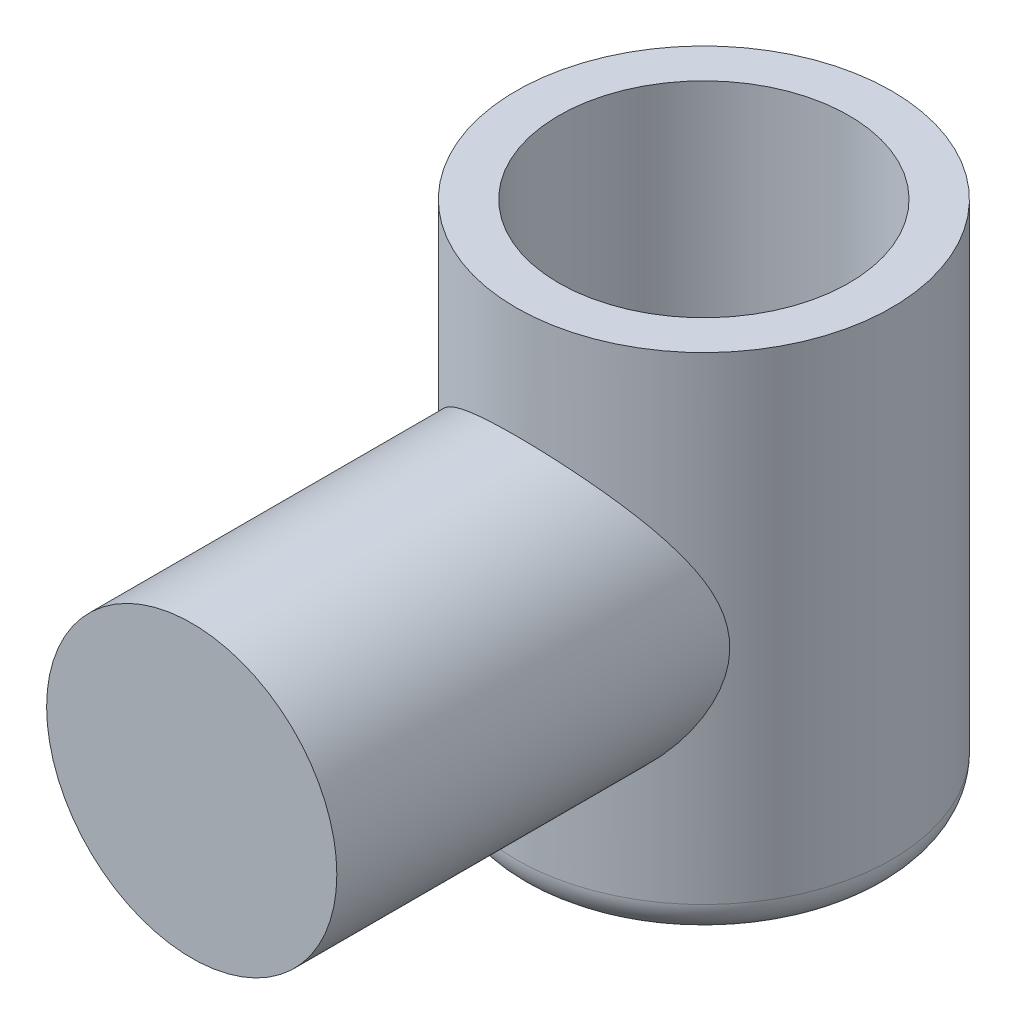
SolidWorks part; units mm, degrees
ref_plane "Front Plane" through (0, 0, 0) normal (0, 0, 1) x (1, 0, 0)
ref_plane "Top Plane" through (0, 0, 0) normal (0, 1, 0) x (1, 0, 0)
ref_plane "Right Plane" through (0, 0, 0) normal (1, 0, 0) x (0, 0, -1)
sketch "Sketch1" plane through (0, 0, 0) normal (0, 1, 0) x (1, 0, 0)
  line L0 (0, -55) -> (0, 55) construction
  line L1 (-55, 0) -> (55, 0) construction
  circle A0 centre (0, 0) radius 55
  dimension "D1" = 110
extrude "Boss-Extrude1" add sketch "Sketch1" along normal mid plane 150
sketch "Sketch2" plane through (0, 0, 0) normal (0, 0, 1) x (1, 0, 0)
  circle A0 centre (0, 0) radius 42.5
  dimension "D1" = 85
extrude "Boss-Extrude2" add sketch "Sketch2" along normal blind 150
fillet "Fillet2" radius 10 1 edges at (0, -75, 55)
sketch "Sketch3" plane through (0, 0, 0) normal (0, 1, 0) x (1, 0, 0)
  circle A0 centre (0, 0) radius 42.5
  dimension "D1" = 85
extrude "Cut-Extrude1" cut sketch "Sketch3" along normal blind 110 contours A0
